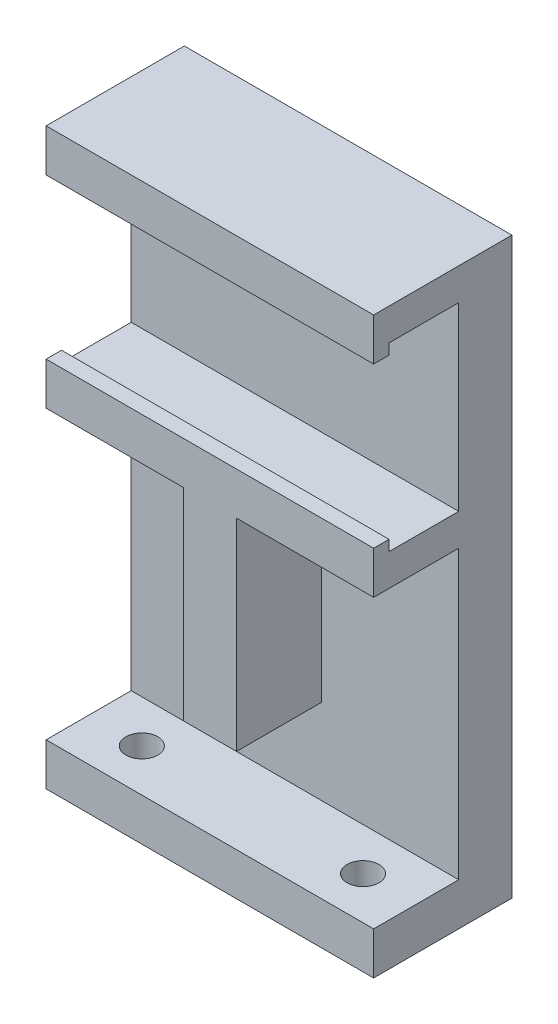
SolidWorks part; units mm, degrees
material "1060 合金"
ref_plane "前视基准面" through (0, 0, 0) normal (0, 0, 1) x (1, 0, 0)
ref_plane "上视基准面" through (0, 0, 0) normal (0, 1, 0) x (1, 0, 0)
ref_plane "右视基准面" through (0, 0, 0) normal (1, 0, 0) x (0, 0, -1)
sketch "草图1" plane through (0, 0, 0) normal (0, 0, 1) x (1, 0, 0)
  line L1 (0, 0) -> (30.8, 0)
  line L2 (0, 0) -> (0, 42)
  line L3 (0, 42) -> (30.8, 42)
  line L4 (30.8, 0) -> (30.8, 42)
  dimension "D1" = 30.8
  dimension "D2" = 42
extrude "凸台-拉伸1" add sketch "草图1" along normal blind 5
sketch "草图2" plane through (0, 0, 5) normal (0, 0, 1) x (1, 0, 0)
  line L0 (-5.69, 30.5) -> (26.1415, 30.5) construction
  line L1 (0, 0) -> (30.8, 0) construction
  line L2 (30.8, 0) -> (30.8, 42) construction
  line L3 (0, 39) -> (0, 42)
  line L4 (0, 42) -> (30.8, 42)
  line L5 (0, 39) -> (30.8, 39)
  line L6 (30.8, 42) -> (30.8, 39)
  line L7 (0, 42) -> (0, 0) construction
  line L8 (0, 22) -> (30.8, 22)
  line L9 (0, 22) -> (0, 19)
  line L10 (0, 19) -> (30.8, 19)
  line L11 (30.8, 22) -> (30.8, 19)
  dimension "D1" = 30.5
  dimension "D2" = 8.5
  dimension "D3" = 8.5
  dimension "D4" = 3
  dimension "D5" = 3
extrude "凸台-拉伸2" add sketch "草图2" along normal blind 8
sketch "草图3" plane through (0, 0, 5) normal (0, 0, 1) x (1, 0, 0)
  line L0 (0, 0) -> (30.8, 0) construction
  line L1 (12.9, 0) -> (17.9, 0)
  line L2 (12.9, 0) -> (12.9, 19)
  line L3 (12.9, 19) -> (17.9, 19)
  line L4 (17.9, 0) -> (17.9, 19)
  line L5 (0, 19) -> (30.8, 19) construction
  point P8 (15.4, 0)
  dimension "D1" = 5
  dimension "D2" = 2.5
extrude "凸台-拉伸3" add sketch "草图3" along normal blind 8
sketch "草图4" plane through (30.8, 0, 0) normal (1, 0, 0) x (0, 0, -1)
  line L0 (-5, 0) -> (-5, -8)
  line L1 (-5, -8) -> (-13, -8)
  line L2 (-13, -8) -> (-13, -12)
  line L3 (-13, -12) -> (0, -12)
  line L4 (0, -12) -> (0, 0)
  line L5 (-5, 0) -> (0, 0)
  dimension "D1" = 8
  dimension "D2" = 4
extrude "凸台-拉伸4" add sketch "草图4" against normal up to surface (30.8 mm away) up to face at (0, 26.2, 7.6)
sketch "草图5" plane through (0, -8, 0) normal (0, 1, 0) x (1, 0, 0)
  line L0 (0, -13) -> (0, -5) construction
  line L1 (30.8, -5) -> (30.8, -13) construction
  line L2 (0, -5) -> (30.8, -5) construction
  circle A0 centre (5, -9) radius 1.5
  circle A1 centre (25.8, -9) radius 1.5
  dimension "D1" = 3
  dimension "D2" = 5
  dimension "D3" = 5
  dimension "D4" = 4
  dimension "D5" = 4
extrude "切除-拉伸1" cut sketch "草图5" against normal up to next
sketch "草图6" plane through (30.8, 0, 0) normal (1, 0, 0) x (0, 0, -1)
  line L1 (-13, 39) -> (-11.55, 39)
  line L2 (-13, 39) -> (-13, 38)
  line L3 (-13, 38) -> (-11.55, 38)
  line L4 (-11.55, 39) -> (-11.55, 38)
  line L5 (-13, 22) -> (-11.55, 22)
  line L6 (-13, 22) -> (-13, 23)
  line L7 (-13, 23) -> (-11.55, 23)
  line L8 (-11.55, 22) -> (-11.55, 23)
  dimension "D1" = 1
  dimension "D2" = 1.45
  dimension "D3" = 1
  dimension "D4" = 1.45
extrude "凸台-拉伸5" add sketch "草图6" against normal through all
